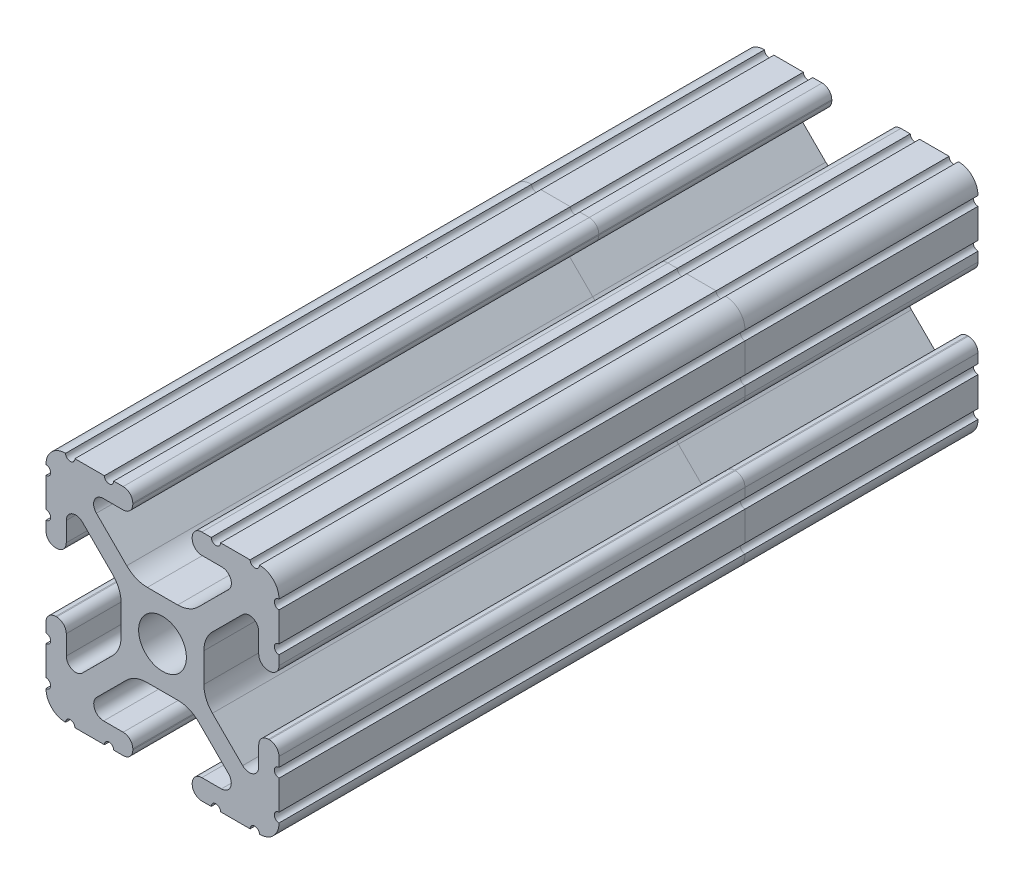
SolidWorks part; units mm, degrees
ref_plane "Front Plane" through (0, 0, 0) normal (0, 0, 1) x (1, 0, 0)
ref_plane "Top Plane" through (0, 0, 0) normal (0, 1, 0) x (1, 0, 0)
ref_plane "Right Plane" through (0, 0, 0) normal (1, 0, 0) x (0, 0, -1)
sketch "Sketch1" plane through (0, 0, 0) normal (0, 0, 1) x (1, 0, 0)
  line L88 (-7.1797, -8.6452) -> (-3.9523, -5.4237)
  line L89 (-1.7093, -4.4958) -> (1.7093, -4.4958)
  line L90 (3.9523, -5.4237) -> (7.1797, -8.6452)
  line L91 (6.4164, -10.4902) -> (4.2875, -10.4902)
  line L92 (3.2385, -11.5392) -> (3.2385, -11.651)
  line L93 (4.2875, -12.7) -> (5.3171, -12.7)
  line L94 (6.3331, -12.7) -> (9.5504, -12.7)
  line L95 (12.7, -9.5504) -> (12.7, -6.3331)
  line L96 (12.7, -5.3171) -> (12.7, -4.2875)
  line L97 (11.651, -3.2385) -> (11.5392, -3.2385)
  line L98 (10.4902, -4.2875) -> (10.4902, -6.4021)
  line L99 (8.7371, -7.1294) -> (5.441, -3.8408)
  line L100 (4.5085, -1.5932) -> (4.5085, 1.5932)
  line L101 (5.441, 3.8408) -> (8.7371, 7.1294)
  line L102 (10.4902, 6.4021) -> (10.4902, 4.2875)
  line L103 (11.5392, 3.2385) -> (11.651, 3.2385)
  line L104 (12.7, 4.2875) -> (12.7, 5.3171)
  line L105 (12.7, 6.3331) -> (12.7, 9.5504)
  line L106 (9.5504, 12.7) -> (6.3331, 12.7)
  line L107 (5.3171, 12.7) -> (4.2875, 12.7)
  line L108 (3.2385, 11.651) -> (3.2385, 11.5392)
  line L109 (4.2875, 10.4902) -> (6.4768, 10.4902)
  line L110 (7.207, 8.7244) -> (3.8983, 5.4232)
  line L111 (1.6558, 4.4958) -> (-1.6558, 4.4958)
  line L112 (-3.8983, 5.4232) -> (-7.207, 8.7244)
  line L113 (-6.4768, 10.4902) -> (-4.2875, 10.4902)
  line L114 (-3.2385, 11.5392) -> (-3.2385, 11.651)
  line L115 (-4.2875, 12.7) -> (-5.3171, 12.7)
  line L116 (-6.3331, 12.7) -> (-9.5504, 12.7)
  line L117 (-12.7, 9.5504) -> (-12.7, 6.3331)
  line L118 (-12.7, 5.3171) -> (-12.7, 4.2875)
  line L119 (-11.651, 3.2385) -> (-11.5392, 3.2385)
  line L120 (-10.4902, 4.2875) -> (-10.4902, 6.4021)
  line L121 (-8.7371, 7.1294) -> (-5.441, 3.8408)
  line L122 (-4.5085, 1.5932) -> (-4.5085, -1.5932)
  line L123 (-5.441, -3.8408) -> (-8.7371, -7.1294)
  line L124 (-10.4902, -6.4021) -> (-10.4902, -4.2875)
  line L125 (-11.5392, -3.2385) -> (-11.651, -3.2385)
  line L126 (-12.7, -4.2875) -> (-12.7, -5.3171)
  line L127 (-12.7, -6.3331) -> (-12.7, -9.5504)
  line L128 (-9.5504, -12.7) -> (-6.3331, -12.7)
  line L129 (-5.3171, -12.7) -> (-4.2875, -12.7)
  line L130 (-3.2385, -11.651) -> (-3.2385, -11.5392)
  line L131 (-4.2875, -10.4902) -> (-6.4164, -10.4902)
  circle A1 centre (0, 0) radius 2.6035
  arc A104 (-7.1797, -8.6452) -> (-6.4164, -10.4902) centre (-6.4164, -9.4098) ccw
  arc A105 (-1.7093, -4.4958) -> (-3.9523, -5.4237) centre (-1.7093, -7.6708) ccw
  arc A106 (3.9523, -5.4237) -> (1.7093, -4.4958) centre (1.7093, -7.6708) ccw
  arc A107 (6.4164, -10.4902) -> (7.1797, -8.6452) centre (6.4164, -9.4098) ccw
  arc A108 (4.2875, -10.4902) -> (3.2385, -11.5392) centre (4.2875, -11.5392) ccw
  arc A109 (3.2385, -11.651) -> (4.2875, -12.7) centre (4.2875, -11.651) ccw
  arc A110 (6.3331, -12.7) -> (5.3171, -12.7) centre (5.8251, -12.7) ccw
  arc A111 (10.5664, -12.6998) -> (9.5504, -12.7) centre (10.0584, -12.7) ccw
  arc A112 (10.5664, -12.6998) -> (12.6998, -10.5664) centre (10.5918, -10.5918) ccw
  arc A113 (12.7, -9.5504) -> (12.6998, -10.5664) centre (12.7, -10.0584) ccw
  arc A114 (12.7, -5.3171) -> (12.7, -6.3331) centre (12.7, -5.8251) ccw
  arc A115 (12.7, -4.2875) -> (11.651, -3.2385) centre (11.651, -4.2875) ccw
  arc A116 (11.5392, -3.2385) -> (10.4902, -4.2875) centre (11.5392, -4.2875) ccw
  arc A117 (8.7371, -7.1294) -> (10.4902, -6.4021) centre (9.4628, -6.4021) ccw
  arc A118 (4.5085, -1.5932) -> (5.441, -3.8408) centre (7.6835, -1.5932) ccw
  arc A119 (5.441, 3.8408) -> (4.5085, 1.5932) centre (7.6835, 1.5932) ccw
  arc A120 (10.4902, 6.4021) -> (8.7371, 7.1294) centre (9.4628, 6.4021) ccw
  arc A121 (10.4902, 4.2875) -> (11.5392, 3.2385) centre (11.5392, 4.2875) ccw
  arc A122 (11.651, 3.2385) -> (12.7, 4.2875) centre (11.651, 4.2875) ccw
  arc A123 (12.7, 6.3331) -> (12.7, 5.3171) centre (12.7, 5.8251) ccw
  arc A124 (12.6998, 10.5664) -> (12.7, 9.5504) centre (12.7, 10.0584) ccw
  arc A125 (12.6998, 10.5664) -> (10.5664, 12.6998) centre (10.5918, 10.5918) ccw
  arc A126 (9.5504, 12.7) -> (10.5664, 12.6998) centre (10.0584, 12.7) ccw
  arc A127 (5.3171, 12.7) -> (6.3331, 12.7) centre (5.8251, 12.7) ccw
  arc A128 (4.2875, 12.7) -> (3.2385, 11.651) centre (4.2875, 11.651) ccw
  arc A129 (3.2385, 11.5392) -> (4.2875, 10.4902) centre (4.2875, 11.5392) ccw
  arc A130 (7.207, 8.7244) -> (6.4768, 10.4902) centre (6.4768, 9.4563) ccw
  arc A131 (1.6558, 4.4958) -> (3.8983, 5.4232) centre (1.6558, 7.6708) ccw
  arc A132 (-3.8983, 5.4232) -> (-1.6558, 4.4958) centre (-1.6558, 7.6708) ccw
  arc A133 (-6.4768, 10.4902) -> (-7.207, 8.7244) centre (-6.4768, 9.4563) ccw
  arc A134 (-4.2875, 10.4902) -> (-3.2385, 11.5392) centre (-4.2875, 11.5392) ccw
  arc A135 (-3.2385, 11.651) -> (-4.2875, 12.7) centre (-4.2875, 11.651) ccw
  arc A136 (-6.3331, 12.7) -> (-5.3171, 12.7) centre (-5.8251, 12.7) ccw
  arc A137 (-10.5664, 12.6998) -> (-9.5504, 12.7) centre (-10.0584, 12.7) ccw
  arc A138 (-10.5664, 12.6998) -> (-12.6998, 10.5664) centre (-10.5918, 10.5918) ccw
  arc A139 (-12.7, 9.5504) -> (-12.6998, 10.5664) centre (-12.7, 10.0584) ccw
  arc A140 (-12.7, 5.3171) -> (-12.7, 6.3331) centre (-12.7, 5.8251) ccw
  arc A141 (-12.7, 4.2875) -> (-11.651, 3.2385) centre (-11.651, 4.2875) ccw
  arc A142 (-11.5392, 3.2385) -> (-10.4902, 4.2875) centre (-11.5392, 4.2875) ccw
  arc A143 (-8.7371, 7.1294) -> (-10.4902, 6.4021) centre (-9.4628, 6.4021) ccw
  arc A144 (-4.5085, 1.5932) -> (-5.441, 3.8408) centre (-7.6835, 1.5932) ccw
  arc A145 (-5.441, -3.8408) -> (-4.5085, -1.5932) centre (-7.6835, -1.5932) ccw
  arc A146 (-10.4902, -6.4021) -> (-8.7371, -7.1294) centre (-9.4628, -6.4021) ccw
  arc A147 (-10.4902, -4.2875) -> (-11.5392, -3.2385) centre (-11.5392, -4.2875) ccw
  arc A148 (-11.651, -3.2385) -> (-12.7, -4.2875) centre (-11.651, -4.2875) ccw
  arc A149 (-12.7, -6.3331) -> (-12.7, -5.3171) centre (-12.7, -5.8251) ccw
  arc A150 (-12.6998, -10.5664) -> (-12.7, -9.5504) centre (-12.7, -10.0584) ccw
  arc A151 (-12.6998, -10.5664) -> (-10.5664, -12.6998) centre (-10.5918, -10.5918) ccw
  arc A152 (-9.5504, -12.7) -> (-10.5664, -12.6998) centre (-10.0584, -12.7) ccw
  arc A153 (-5.3171, -12.7) -> (-6.3331, -12.7) centre (-5.8251, -12.7) ccw
  arc A154 (-4.2875, -12.7) -> (-3.2385, -11.651) centre (-4.2875, -11.651) ccw
  arc A155 (-3.2385, -11.5392) -> (-4.2875, -10.4902) centre (-4.2875, -11.5392) ccw
extrude "Boss-Extrude1" add sketch "Sketch1" along normal mid plane 76.2
ref_plane "Plane1" through (0, 0, -12.7) normal (0, 0, -1) x (-1, 0, 0)
split "Split1" trim tools "Plane1" bodies to split 103 resulting bodies 105 106
